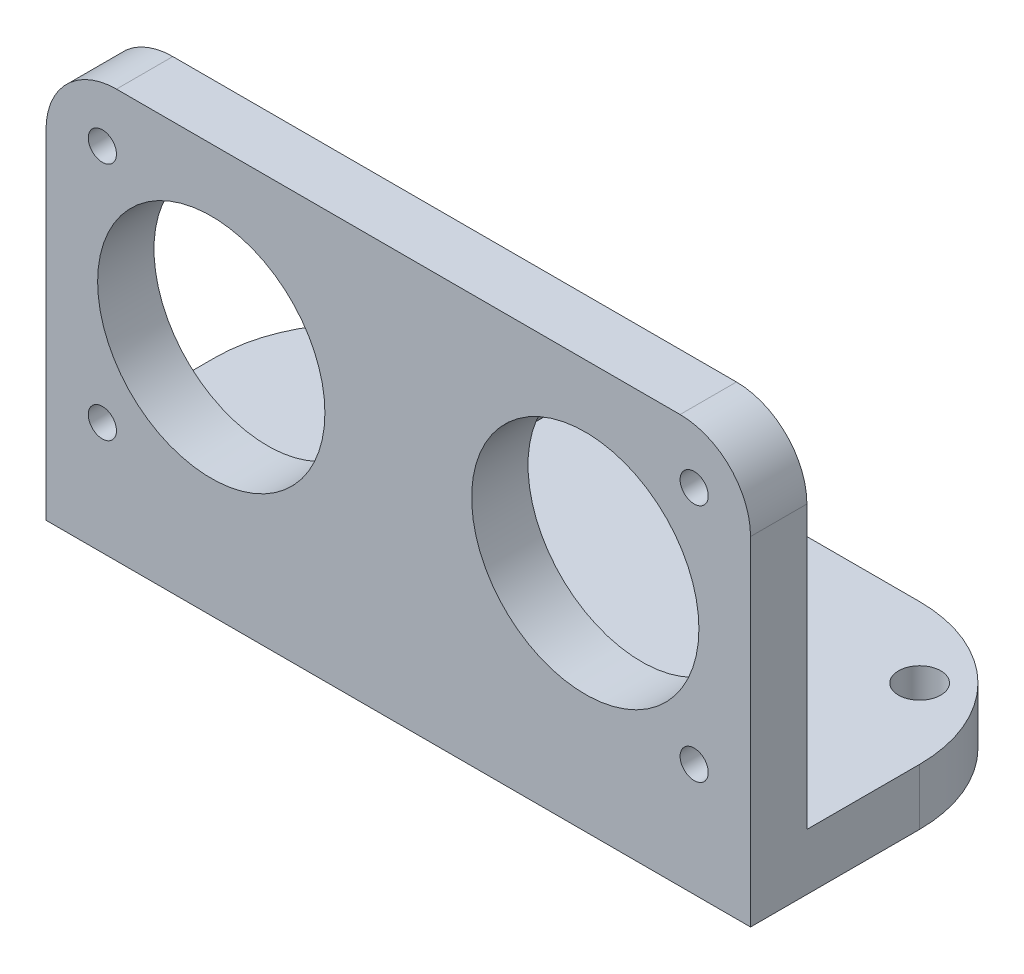
SolidWorks part; units mm, degrees
ref_plane "Front Plane" through (0, 0, 0) normal (0, 0, 1) x (1, 0, 0)
ref_plane "Top Plane" through (0, 0, 0) normal (0, 1, 0) x (1, 0, 0)
ref_plane "Right Plane" through (0, 0, 0) normal (1, 0, 0) x (0, 0, -1)
sketch "Sketch1" plane through (0, 0, 0) normal (0, 0, 1) x (1, 0, 0)
  line L1 (-25, 12.5) -> (25, 12.5)
  line L2 (-25, 12.5) -> (-25, -12.5)
  line L3 (-25, -12.5) -> (25, -12.5)
  line L4 (25, 12.5) -> (25, -12.5)
  line L5 (-25, 12.5) -> (25, -12.5) construction
  line L6 (-25, -12.5) -> (25, 12.5) construction
  point P0 (0, 0)
  dimension "D1" = 50
  dimension "D2" = 25
extrude "Boss-Extrude1" add sketch "Sketch1" along normal blind 4
sketch "Sketch2" plane through (0, -12.5, 0) normal (0, -1, 0) x (1, 0, 0)
  line L1 (25, -18) -> (-25, -18)
  line L2 (25, -18) -> (25, 4)
  line L3 (25, 4) -> (-25, 4)
  line L4 (-25, -18) -> (-25, 4)
  line L5 (25, -18) -> (-25, 4) construction
  line L6 (25, 4) -> (-25, -18) construction
  point P0 (0, -7)
  dimension "D1" = 22
extrude "Boss-Extrude2" add sketch "Sketch2" along normal blind 4
sketch "Sketch3" plane through (0, 0, 4) normal (0, 0, 1) x (1, 0, 0)
  line L0 (0, 12.5) -> (0, -12.5) construction
  line L1 (-25, -12.5) -> (25, -12.5) construction
  line L2 (-25, -12.5) -> (-25, 12.5) construction
  line L3 (-25, 12.5) -> (25, 12.5) construction
  line L4 (25, -12.5) -> (25, 12.5) construction
  line L5 (-25, -12.5) -> (25, 12.5) construction
  line L6 (-25, 12.5) -> (25, -12.5) construction
  line L7 (0, 0) -> (25, 0) construction
  circle A0 centre (13.2715, 0) radius 8.0645
  point P0 (0, 0)
  point P14 (5.207, 0)
  dimension "D1" = 16.129
  dimension "D2" = 5.207
extrude "Cut-Extrude1" cut sketch "Sketch3" against normal through all contours A0
mirror "Mirror1" about plane through (0, 0, 0) normal (1, 0, 0) of "Cut-Extrude1"
sketch "Sketch4" plane through (0, 0, 0) normal (0, 0, -1) x (-1, 0, 0)
  circle A0 centre (0, 0) radius 2
  dimension "D1" = 4
extrude "Boss-Extrude4" add sketch "Sketch4" along normal blind 5
hole_wizard "Ø3.0mm Dowel Hole1" positions "Sketch5" profile "Sketch6" hole size "Ø3.0" standard "ANSI Metric" end condition through all
sketch "Sketch5" plane through (0, -12.5, 0) normal (0, 1, 0) x (1, 0, 0)
  line L0 (-20, 13) -> (-25, 13) construction
  line L1 (-25, 0) -> (-25, 18) construction
  line L3 (-20, 13) -> (-20, 18) construction
  line L4 (-25, 18) -> (25, 18) construction
  point P0 (-20, 13)
  dimension "D1" = 5
  dimension "D2" = 5
sketch "Sketch6" plane through (-20, -12.5, -13) normal (1, 0, 0) x (0, 0, 1)
  line L0 (0, 0) -> (0, 4)
  line L1 (0, 4) -> (1.5, 4)
  line L2 (1.5, 4) -> (1.5, 0)
  line L5 (1.5, 0) -> (0, 0)
  line L11 (0, -6.35) -> (0, 107.95) construction
  dimension "Thru Hole Dia." = 3
  dimension "Thru Hole Depth" = 4
mirror "Mirror2" about plane through (0, 0, 0) normal (1, 0, 0) of "Ø3.0mm Dowel Hole1"
hole_wizard "Ø2.0mm Dowel Hole1" positions "Sketch7" profile "Sketch8" hole size "Ø2.0" standard "ANSI Metric" end condition through all
sketch "Sketch7" plane through (0, 0, 0) normal (0, 0, -1) x (-1, 0, 0)
  line L0 (-21, 12.5) -> (-21, 8.5) construction
  line L1 (-25, 12.5) -> (25, 12.5) construction
  line L2 (-21, 8.5) -> (-25, 8.5) construction
  line L3 (-25, -12.5) -> (-25, 12.5) construction
  point P0 (-21, 8.5)
  dimension "D1" = 4
  dimension "D2" = 4
sketch "Sketch8" plane through (21, 8.5, 0) normal (1, 0, 0) x (0, 1, 0)
  line L0 (0, 0) -> (0, 4)
  line L1 (0, 4) -> (1, 4)
  line L2 (1, 4) -> (1, 0)
  line L5 (1, 0) -> (0, 0)
  line L11 (0, -6.35) -> (0, 107.95) construction
  dimension "Thru Hole Dia." = 2
  dimension "Thru Hole Depth" = 4
mirror "Mirror3" about plane through (0, 0, 0) normal (0, 1, 0) of "Ø2.0mm Dowel Hole1"
mirror "Mirror4" about plane through (0, 0, 0) normal (1, 0, 0) of "Mirror3", "Ø2.0mm Dowel Hole1"
fillet "Fillet1" radius 10 2 edges at (25, -14.5, -18) (-25, -14.5, -18)
fillet "Fillet2" radius 5 2 edges at (25, 12.5, 2) (-25, 12.5, 2)
